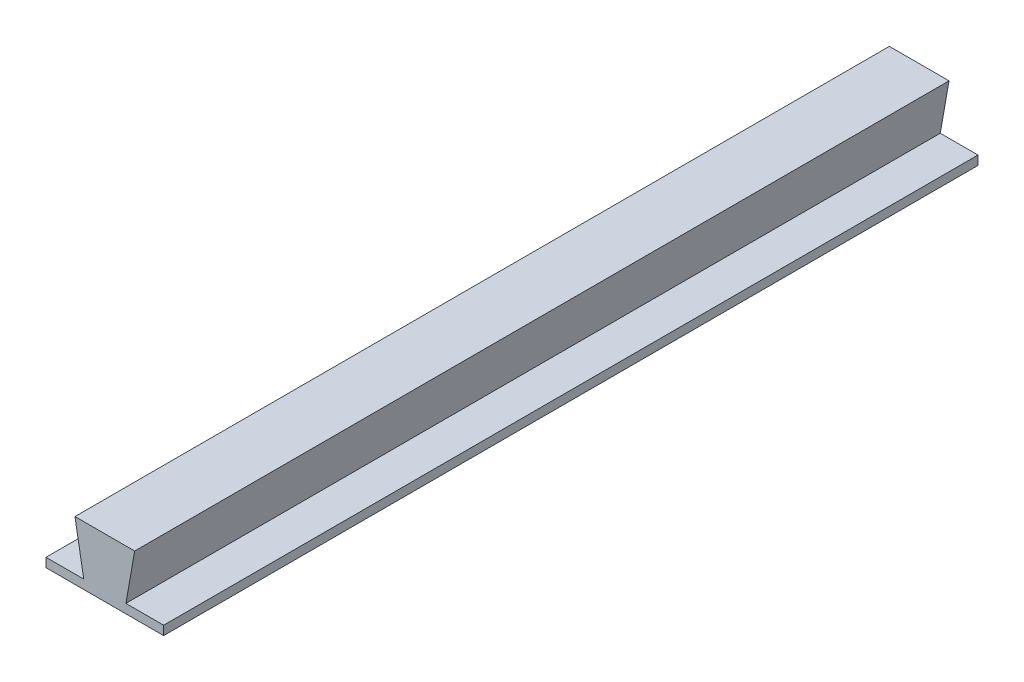
SolidWorks part; units mm, degrees
ref_plane "Front Plane" through (0, 0, 0) normal (0, 0, 1) x (1, 0, 0)
ref_plane "Top Plane" through (0, 0, 0) normal (0, 1, 0) x (1, 0, 0)
ref_plane "Right Plane" through (0, 0, 0) normal (1, 0, 0) x (0, 0, -1)
sketch "Sketch1" plane through (0, 0, 0) normal (0, 0, 1) x (1, 0, 0)
  line L0 (0, 30.7054) -> (0, -29.0356) construction
  line L1 (-4.6604, 0) -> (4.6604, 0)
  line L2 (4.6604, 0) -> (6.6, 11)
  line L3 (6.6, 11) -> (-6.6, 11)
  line L4 (0, 11) -> (0, 0)
  line L5 (-4.6604, 0) -> (-6.6, 11)
  dimension "D1" = 80
  dimension "D2" = 6.6
  dimension "D3" = 11
extrude "Boss-Extrude1" add sketch "Sketch1" along normal blind 180 contours L5 L1 L4 L3 | L3 L4 L1 L2
sketch "Sketch2" plane through (0, 0, 0) normal (0, -1, 0) x (1, 0, 0)
  line L0 (0, 180) -> (0, 0) construction
  line L1 (-4.6604, 180) -> (4.6604, 180) construction
  line L2 (-4.6604, 0) -> (4.6604, 0) construction
  line L4 (-13, 0) -> (13, 0)
  line L5 (-13, 0) -> (-13, 180)
  line L6 (-13, 180) -> (13, 180)
  line L7 (13, 0) -> (13, 180)
  line L8 (-13, 0) -> (13, 180) construction
  line L9 (-13, 180) -> (13, 0) construction
  point P6 (0, 90)
  point P11 (13, 180)
  dimension "D1" = 26
extrude "Boss-Extrude2" add sketch "Sketch2" along normal blind 2
